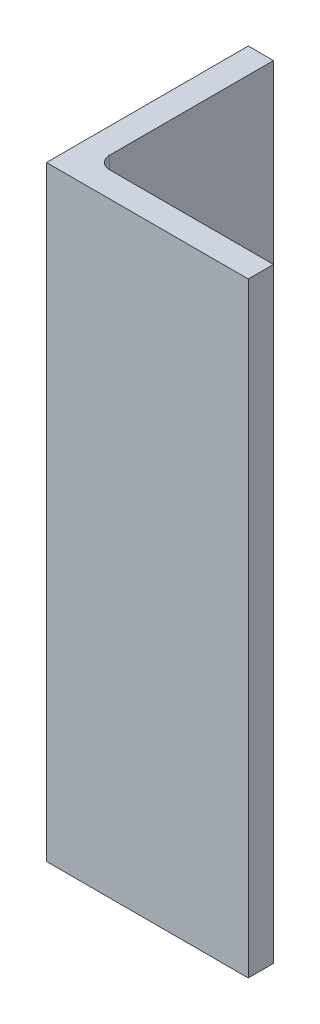
SolidWorks part; units mm, degrees
ref_plane "Front Plane" through (0, 0, 0) normal (0, 0, 1) x (1, 0, 0)
ref_plane "Top Plane" through (0, 0, 0) normal (0, 1, 0) x (1, 0, 0)
ref_plane "Right Plane" through (0, 0, 0) normal (1, 0, 0) x (0, 0, -1)
sketch "Sketch1" plane through (0, 0, 0) normal (0, 1, 0) x (1, 0, 0)
  line L0 (0, 0) -> (0, 50.8)
  line L1 (0, 50.8) -> (6.35, 50.8)
  line L2 (6.35, 50.8) -> (6.35, 6.35)
  line L3 (6.35, 6.35) -> (50.8, 6.35)
  line L4 (50.8, 6.35) -> (50.8, 0)
  line L5 (50.8, 0) -> (0, 0)
  dimension "D1" = 6.35
  dimension "D2" = 50.8
  dimension "D3" = 50.8
extrude "Boss-Extrude1" add sketch "Sketch1" along normal blind 152.4
fillet "Fillet1" radius 3.175 1 edges at (6.35, 76.2, -6.35)
hole_wizard "3/4 (0.75) Diameter Hole1" positions "Sketch3" profile "Sketch4" hole size "3/4" standard "Ansi Inch" end condition up to next
sketch "Sketch3" plane through (0, 0, 0) normal (-1, 0, 0) x (0, 0, 1)
  line L0 (-50.8, 152.4) -> (0, 152.4) construction
  line L2 (-50.8, 152.4) -> (-50.8, 0) construction
  point P0 (-25.4, 31.75)
  dimension "D1" = 120.65
  dimension "D2" = 25.4
sketch "Sketch4" plane through (0, 31.75, -25.4) normal (0, 1, 0) x (0, 0, 1)
  line L0 (0, 0) -> (0, 6.35)
  line L1 (0, 6.35) -> (9.525, 6.35)
  line L2 (9.525, 6.35) -> (9.525, 0)
  line L5 (9.525, 0) -> (0, 0)
  line L11 (0, -6.35) -> (0, 107.95) construction
  dimension "Thru Hole Dia." = 19.05
  dimension "Thru Hole Depth" = 6.35
